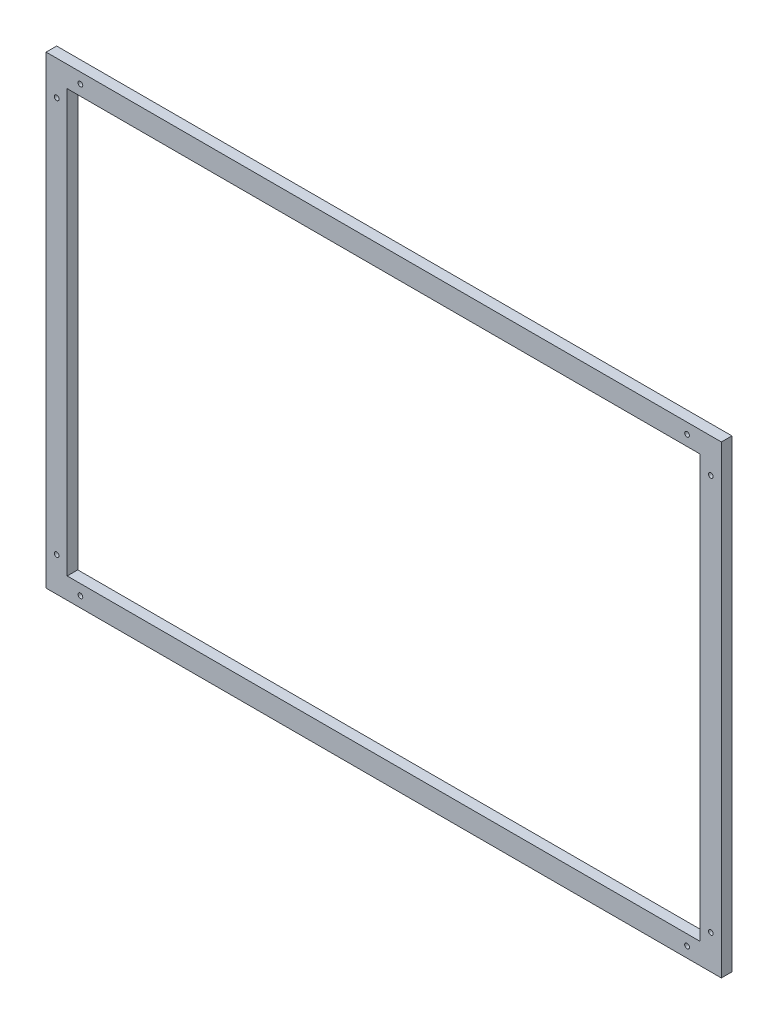
SolidWorks part; units mm, degrees
ref_plane "Plan de face" through (0, 0, 0) normal (0, 0, 1) x (1, 0, 0)
ref_plane "Plan de dessus" through (0, 0, 0) normal (0, 1, 0) x (1, 0, 0)
ref_plane "Plan de droite" through (0, 0, 0) normal (1, 0, 0) x (0, 0, -1)
sketch "Esquisse1" plane through (0, 0, 0) normal (0, 0, 1) x (1, 0, 0)
  line L1 (0, 0) -> (-640, 0)
  line L2 (0, 0) -> (0, 440)
  line L3 (0, 440) -> (-640, 440)
  line L4 (-640, 0) -> (-640, 440)
  line L5 (-620, 420) -> (-20, 420)
  line L6 (-620, 420) -> (-620, 20)
  line L7 (-620, 20) -> (-20, 20)
  line L8 (-20, 420) -> (-20, 20)
  dimension "D1" = 640
  dimension "D2" = 440
  dimension "D3" = 20
  dimension "D4" = 20
  dimension "D5" = 20
  dimension "D6" = 20
extrude "Boss.-Extru.1" add sketch "Esquisse1" along normal blind 10
sketch "Esquisse2" plane through (0, 0, 10) normal (0, 0, 1) x (1, 0, 0)
  line L0 (0, 0) -> (0, 440) construction
  line L1 (0, 440) -> (-640, 440) construction
  line L2 (-20, 420) -> (-620, 420) construction
  line L3 (-640, 0) -> (0, 0) construction
  line L4 (-620, 20) -> (-20, 20) construction
  line L5 (-640, 440) -> (-640, 0) construction
  line L6 (-620, 420) -> (-620, 20) construction
  circle A0 centre (-32.5, 430) radius 2.25
  circle A1 centre (-10, 407.5) radius 2.25
  circle A2 centre (-607.5, 430) radius 2.25
  circle A3 centre (-630, 407.5) radius 2.25
  circle A4 centre (-630, 32.5) radius 2.25
  circle A5 centre (-607.5, 10) radius 2.25
  circle A6 centre (-32.5, 10) radius 2.25
  circle A7 centre (-10, 32.5) radius 2.25
  dimension "D1" = 4.5
  dimension "D2" = 4.5
  dimension "D3" = 32.5
  dimension "D4" = 32.5
  dimension "D5" = 10
  dimension "D6" = 10
  dimension "D7" = 4.5
  dimension "D8" = 4.5
  dimension "D9" = 32.5
  dimension "D10" = 32.5
  dimension "D11" = 10
  dimension "D12" = 10
  dimension "D13" = 4.5
  dimension "D14" = 32.5
  dimension "D15" = 32.5
  dimension "D16" = 4.5
  dimension "D17" = 10
  dimension "D18" = 10
  dimension "D19" = 4.5
  dimension "D20" = 4.5
  dimension "D21" = 10
  dimension "D22" = 10
  dimension "D23" = 32.5
  dimension "D24" = 32.5
extrude "Enlèv. mat.-Extru.1" cut sketch "Esquisse2" against normal through all
